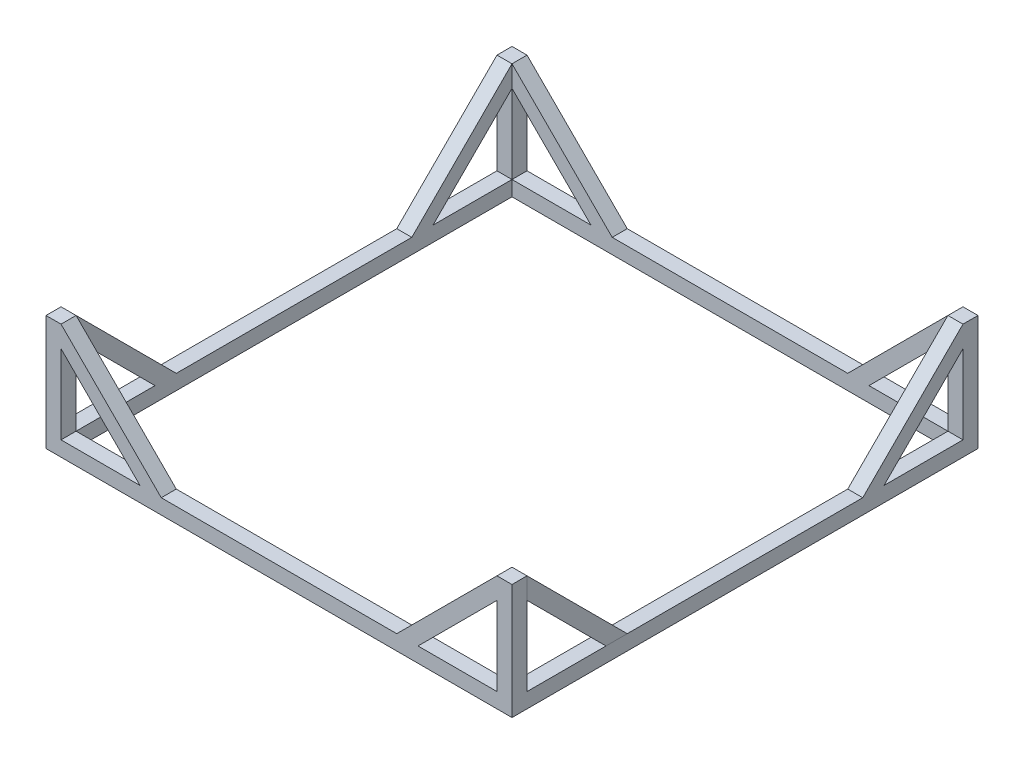
SolidWorks part; units mm, degrees
ref_plane "Front Plane" through (0, 0, 0) normal (0, 0, 1) x (1, 0, 0)
ref_plane "Top Plane" through (0, 0, 0) normal (0, 1, 0) x (1, 0, 0)
ref_plane "Right Plane" through (0, 0, 0) normal (1, 0, 0) x (0, 0, -1)
sketch "Sketch1" plane through (0, 0, 0) normal (0, 1, 0) x (1, 0, 0)
  line L0 (-435, 435) -> (435, 435)
  line L1 (-465, -465) -> (465, -465)
  line L2 (-465, -465) -> (-465, 465)
  line L3 (-465, 465) -> (465, 465)
  line L4 (465, -465) -> (465, 465)
  line L5 (-465, -465) -> (465, 465) construction
  line L6 (-465, 465) -> (465, -465) construction
  line L7 (435, -435) -> (435, 435)
  line L8 (-435, -435) -> (435, -435)
  line L9 (-435, -435) -> (-435, 435)
  point P0 (0, 0)
  dimension "D1" = 930
  dimension "D2" = 930
  dimension "D3" = 30
extrude "Boss-Extrude1" add sketch "Sketch1" along normal blind 30
sketch "Sketch2" plane through (0, 30, 0) normal (0, 1, 0) x (1, 0, 0)
  line L1 (-465, 465) -> (-435, 465)
  line L2 (-465, 465) -> (-465, 435)
  line L3 (-465, 435) -> (-435, 435)
  line L4 (-435, 465) -> (-435, 435)
  line L5 (465, 465) -> (435, 465)
  line L6 (465, 465) -> (465, 435)
  line L7 (465, 435) -> (435, 435)
  line L8 (435, 465) -> (435, 435)
  line L9 (465, -465) -> (435, -465)
  line L10 (465, -465) -> (465, -435)
  line L11 (465, -435) -> (435, -435)
  line L12 (435, -465) -> (435, -435)
  line L13 (-465, -465) -> (-435, -465)
  line L14 (-465, -465) -> (-465, -435)
  line L15 (-465, -435) -> (-435, -435)
  line L16 (-435, -465) -> (-435, -435)
extrude "Boss-Extrude2" add sketch "Sketch2" along normal blind 200
sketch "Sketch4" plane through (-465, 0, 0) normal (-1, 0, 0) x (0, 0, 1)
  line L0 (435, 187.5736) -> (277.4264, 30)
  line L1 (-435, 30) -> (435, 30) construction
  line L2 (435, 230) -> (235, 30)
  line L3 (435, 230) -> (435, 30) construction
  line L4 (435, 187.5736) -> (435, 230)
  line L5 (235, 30) -> (277.4264, 30)
  line L6 (277.4264, 30) -> (256.2132, 51.2132) construction
  dimension "D1" = 200
  dimension "D2" = 30
extrude "Boss-Extrude3" add sketch "Sketch4" against normal blind 30
sketch "Sketch5" plane through (-465, 0, 0) normal (-1, 0, 0) x (0, 0, 1)
  line L0 (-435, 187.5736) -> (-435, 230)
  line L1 (-435, 230) -> (-435, 30) construction
  line L2 (-435, 230) -> (-235, 30)
  line L3 (-435, 30) -> (235, 30) construction
  line L4 (-235, 30) -> (-277.4264, 30)
  line L5 (-277.4264, 30) -> (-435, 187.5736)
  dimension "D1" = 200
  dimension "D2" = 30
extrude "Boss-Extrude4" add sketch "Sketch5" against normal blind 30
sketch "Sketch6" plane through (0, 0, -465) normal (0, 0, -1) x (-1, 0, 0)
  line L0 (435, 230) -> (235, 30)
  line L1 (-435, 30) -> (435, 30) construction
  line L2 (235, 30) -> (277.4264, 30)
  line L3 (277.4264, 30) -> (435, 187.5736)
  line L4 (435, 230) -> (435, 30) construction
  line L5 (435, 187.5736) -> (435, 230)
  dimension "D1" = 200
  dimension "D2" = 30
extrude "Boss-Extrude5" add sketch "Sketch6" against normal blind 30
sketch "Sketch7" plane through (0, 0, -465) normal (0, 0, -1) x (-1, 0, 0)
  line L0 (-435, 230) -> (-235, 30)
  line L1 (-435, 30) -> (235, 30) construction
  line L2 (-235, 30) -> (-277.4264, 30)
  line L3 (-277.4264, 30) -> (-435, 187.5736)
  line L4 (-435, 230) -> (-435, 30) construction
  line L5 (-435, 187.5736) -> (-435, 230)
  dimension "D1" = 30
  dimension "D2" = 200
extrude "Boss-Extrude6" add sketch "Sketch7" against normal blind 30
sketch "Sketch8" plane through (0, 0, 465) normal (0, 0, 1) x (1, 0, 0)
  line L0 (-435, 230) -> (-235, 30)
  line L1 (-435, 30) -> (435, 30) construction
  line L2 (-235, 30) -> (-277.4264, 30)
  line L3 (-277.4264, 30) -> (-435, 187.5736)
  line L4 (-435, 230) -> (-435, 30) construction
  line L5 (-435, 187.5736) -> (-435, 230)
  dimension "D1" = 30
  dimension "D2" = 200
extrude "Boss-Extrude7" add sketch "Sketch8" against normal blind 30
sketch "Sketch9" plane through (0, 0, 465) normal (0, 0, 1) x (1, 0, 0)
  line L0 (435, 230) -> (235, 30)
  line L1 (-235, 30) -> (435, 30) construction
  line L2 (235, 30) -> (277.4264, 30)
  line L3 (277.4264, 30) -> (435, 187.5736)
  line L4 (435, 230) -> (435, 30) construction
  line L5 (435, 187.5736) -> (435, 230)
  dimension "D1" = 30
  dimension "D2" = 200
extrude "Boss-Extrude8" add sketch "Sketch9" against normal blind 30
sketch "Sketch10" plane through (465, 0, 0) normal (1, 0, 0) x (0, 0, -1)
  line L0 (-435, 230) -> (-235, 30)
  line L1 (-435, 30) -> (435, 30) construction
  line L2 (-235, 30) -> (-277.4264, 30)
  line L3 (-277.4264, 30) -> (-435, 187.5736)
  line L4 (-435, 230) -> (-435, 30) construction
  line L5 (-435, 187.5736) -> (-435, 230)
  dimension "D1" = 30
  dimension "D2" = 200
extrude "Boss-Extrude9" add sketch "Sketch10" against normal blind 30 separate body
sketch "Sketch11" plane through (465, 0, 0) normal (1, 0, 0) x (0, 0, -1)
  line L0 (435, 230) -> (235, 30)
  line L1 (-435, 30) -> (435, 30) construction
  line L2 (235, 30) -> (277.4264, 30)
  line L3 (277.4264, 30) -> (435, 187.5736)
  line L4 (435, 230) -> (435, 30) construction
  line L5 (435, 187.5736) -> (435, 230)
  dimension "D1" = 30
  dimension "D2" = 200
extrude "Boss-Extrude10" add sketch "Sketch11" against normal blind 30
